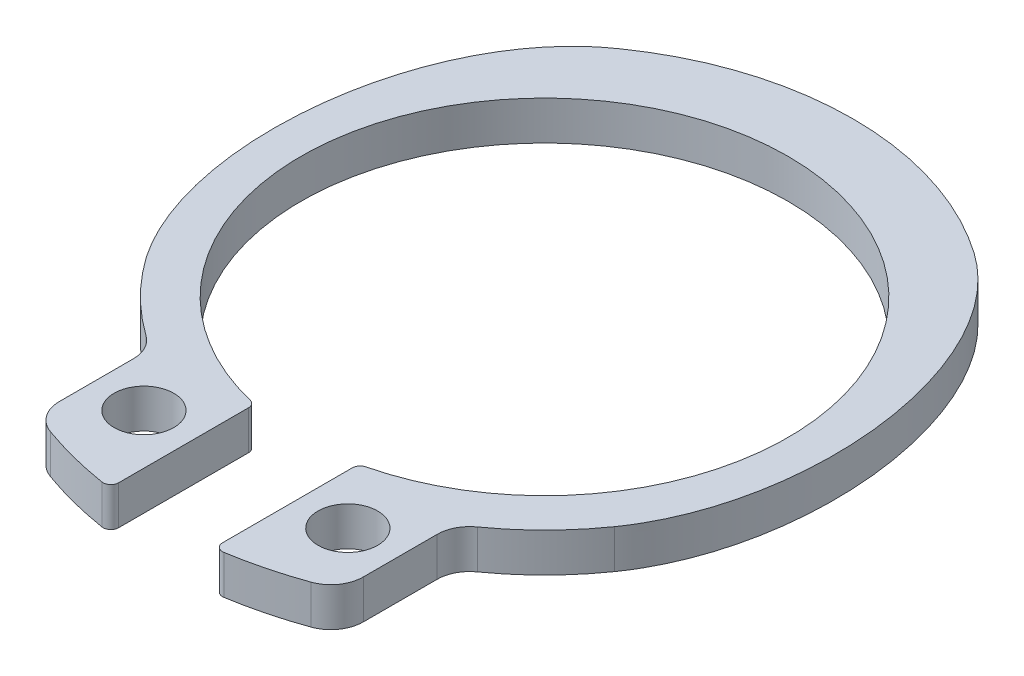
SolidWorks part; units mm, degrees
material "AISI 304"
ref_plane "Front Plane" through (0, 0, 0) normal (0, 0, 1) x (1, 0, 0)
ref_plane "Top Plane" through (0, 0, 0) normal (0, 1, 0) x (1, 0, 0)
ref_plane "Right Plane" through (0, 0, 0) normal (1, 0, 0) x (0, 0, -1)
ref_plane "Piano1" through (0, -0.3, 0) normal (0, -1, 0) x (1, 0, 0)
sketch "Schizzo1" plane through (0, -0.3, 0) normal (0, -1, 0) x (1, 0, 0)
  line L0 (-2.34, 5.13) -> (-2.34, 3.993)
  line L1 (2.34, 3.993) -> (2.34, 5.13)
  line L2 (0.8, 5.757) -> (0.8, 3.7591)
  line L3 (-0.8, 3.7591) -> (-0.8, 5.757)
  circle A0 centre (1.57, 4.5984) radius 0.459
  circle A1 centre (-1.57, 4.5984) radius 0.459
  arc A2 (-0.8, 5.757) -> (-0.9389, 5.8754) centre (-0.92, 5.757) ccw
  arc A3 (-0.9389, 5.8754) -> (-2.0088, 5.6006) centre (0, 0) ccw
  arc A4 (-2.0088, 5.6006) -> (-2.34, 5.13) centre (-1.84, 5.13) ccw
  arc A5 (-2.34, 3.993) -> (-2.5502, 3.5856) centre (-2.84, 3.993) cw
  arc A6 (-2.5502, 3.5856) -> (-3.6043, 2.5237) centre (0, 0) ccw
  arc A7 (-2.7245, -3.891) -> (2.7245, -3.891) centre (0, 0) ccw
  arc A8 (3.6043, 2.5237) -> (2.5502, 3.5856) centre (0, 0) ccw
  arc A9 (2.5502, 3.5856) -> (2.34, 3.993) centre (2.84, 3.993) cw
  arc A10 (2.34, 5.13) -> (2.0088, 5.6006) centre (1.84, 5.13) ccw
  arc A11 (2.0088, 5.6006) -> (0.9389, 5.8754) centre (0, 0) ccw
  arc A12 (0.9389, 5.8754) -> (0.8, 5.757) centre (0.92, 5.757) ccw
  arc A13 (0.8, 3.7591) -> (0.8915, 3.6425) centre (0.92, 3.7591) ccw
  arc A14 (0.8915, 3.6425) -> (-0.8915, 3.6425) centre (0, 0) cw
  arc A15 (-0.8915, 3.6425) -> (-0.8, 3.7591) centre (-0.92, 3.7591) ccw
  spline S0 degree 3 poles (-3.6043, 2.5237) (-3.8539, 2.1569) (-4.0295, 1.7358) (-4.1452, 1.3075) (-4.3082, 0.7037) (-4.3607, 0.0636) (-4.3201, -0.5604) (-4.2786, -1.2001) (-4.1374, -1.8459) (-3.8777, -2.432) (-3.7236, -2.7797) (-3.5233, -3.1131) (-3.2734, -3.3997) (-3.1121, -3.5848) (-2.9275, -3.7528) (-2.7245, -3.891) knots 0 0 0 0 0.001331 0.001331 0.001331 0.003212 0.003212 0.003212 0.005143 0.005143 0.005143 0.00628 0.00628 0.00628 0.007011 0.007011 0.007011 0.007011
  spline S1 degree 3 poles (2.7245, -3.891) (3.0226, -3.6823) (3.2801, -3.4094) (3.4881, -3.1108) (3.7652, -2.7129) (3.9667, -2.2579) (4.1035, -1.7927) (4.2891, -1.1613) (4.364, -0.4888) (4.3311, 0.1685) (4.3042, 0.7076) (4.2036, 1.252) (4.0085, 1.7553) (3.904, 2.0252) (3.7703, 2.2867) (3.6043, 2.5237) knots 0 0 0 0 0.001092 0.001092 0.001092 0.002548 0.002548 0.002548 0.00453 0.00453 0.00453 0.006152 0.006152 0.006152 0.007015 0.007015 0.007015 0.007015
extrude "Estrusione-Estrusione1" add sketch "Schizzo1" against normal blind 0.6
